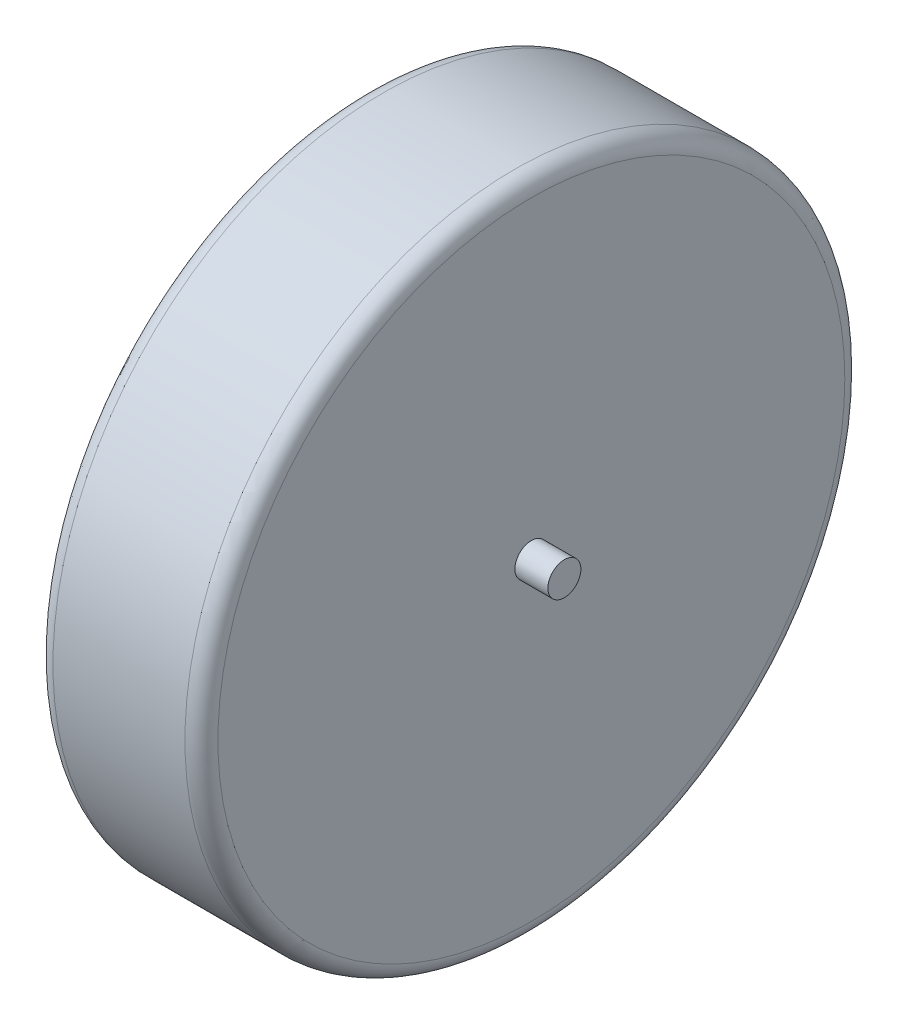
SolidWorks part; units mm, degrees
ref_plane "Front Plane" through (0, 0, 0) normal (0, 0, 1) x (1, 0, 0)
ref_plane "Top Plane" through (0, 0, 0) normal (0, 1, 0) x (1, 0, 0)
ref_plane "Right Plane" through (0, 0, 0) normal (1, 0, 0) x (0, 0, -1)
sketch "Sketch1" plane through (0, 0, 0) normal (1, 0, 0) x (0, 0, -1)
  circle A0 centre (0, 0) radius 20
  dimension "D1" = 40
extrude "Boss-Extrude1" add sketch "Sketch1" along normal blind 10
sketch "Sketch2" plane through (10, 0, 0) normal (1, 0, 0) x (0, 0, -1)
  circle A0 centre (0, 0) radius 1
  dimension "D1" = 2
extrude "Boss-Extrude2" add sketch "Sketch2" along normal blind 2
sketch "Sketch3" plane through (0, 0, 0) normal (-1, 0, 0) x (0, 0, 1)
  circle A0 centre (0, 0) radius 1
  dimension "D1" = 2
extrude "Boss-Extrude3" add sketch "Sketch3" along normal blind 2
fillet "Fillet2" radius 1 2 edges at (10, 0, -20) (0, 0, -20)
